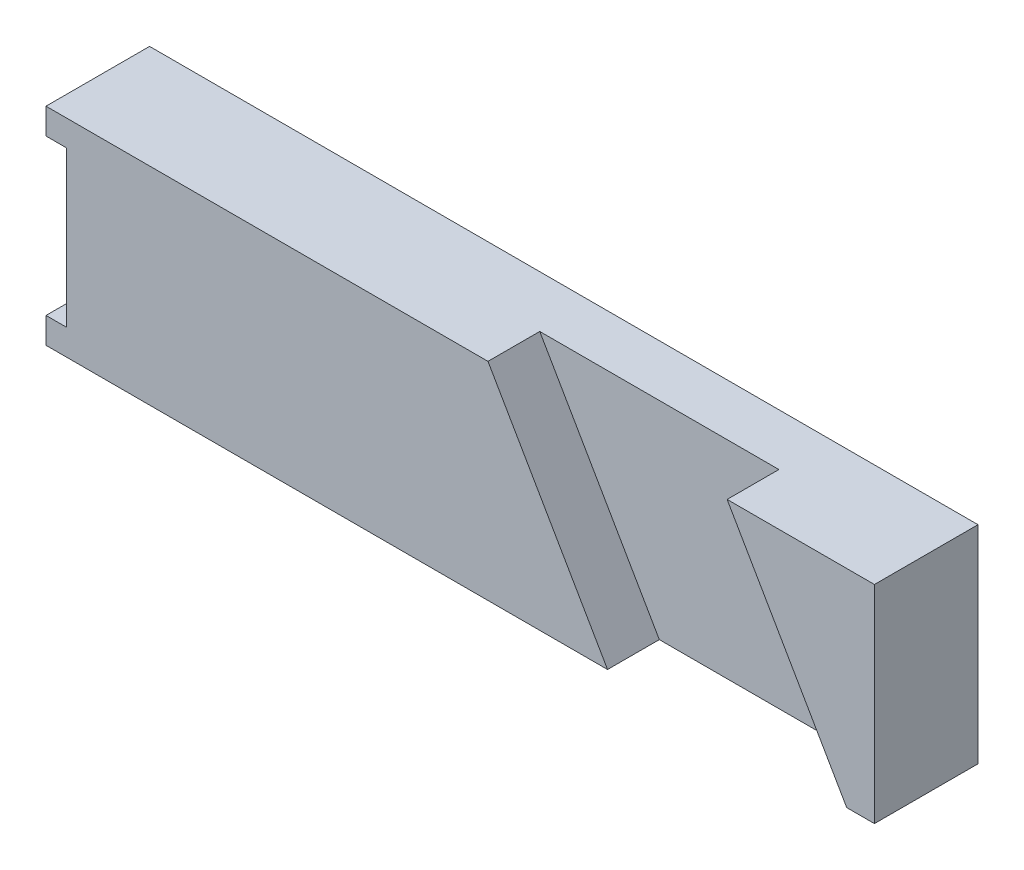
SolidWorks part; units mm, degrees
ref_plane "前基準面" through (0, 0, 0) normal (0, 0, 1) x (1, 0, 0)
ref_plane "上基準面" through (0, 0, 0) normal (0, 1, 0) x (1, 0, 0)
ref_plane "右基準面" through (0, 0, 0) normal (1, 0, 0) x (0, 0, -1)
sketch "草圖2" plane through (0, 0, 0) normal (0, 0, 1) x (1, 0, 0)
  line L0 (-40, 7.5) -> (-38, 7.5)
  line L1 (-40, -10) -> (40, -10)
  line L2 (-40, -10) -> (-40, -7.5)
  line L3 (-40, 10) -> (40, 10)
  line L4 (40, -10) -> (40, 10)
  line L5 (-40, -10) -> (40, 10) construction
  line L6 (-40, 10) -> (40, -10) construction
  line L7 (-38, 7.5) -> (-38, -7.5)
  line L8 (-38, -7.5) -> (-40, -7.5)
  line L9 (-40, 7.5) -> (-40, 10)
  point P0 (0, 0)
  point P10 (-38, 0)
  dimension "D1" = 20
  dimension "D2" = 80
  dimension "D3" = 15
  dimension "D4" = 2
extrude "填料-伸長1" add sketch "草圖2" along normal blind 10
sketch "草圖3" plane through (0, 0, 10) normal (0, 0, 1) x (1, 0, 0)
  line L0 (2.6795, 10) -> (14.2265, -10)
  line L1 (40, 10) -> (-40, 10) construction
  line L2 (-40, -10) -> (40, -10) construction
  line L3 (25.7735, 10) -> (37.3205, -10)
  line L4 (2.6795, 10) -> (37.3205, -10) construction
  line L5 (25.7735, 10) -> (14.2265, -10) construction
  line L6 (2.6795, 10) -> (25.7735, 10)
  line L7 (37.3205, -10) -> (14.2265, -10)
  point P8 (20, 0)
  dimension "D1" = 120
  dimension "D2" = 20
  dimension "D3" = 60
extrude "除料-伸長1" cut sketch "草圖3" against normal blind 5
